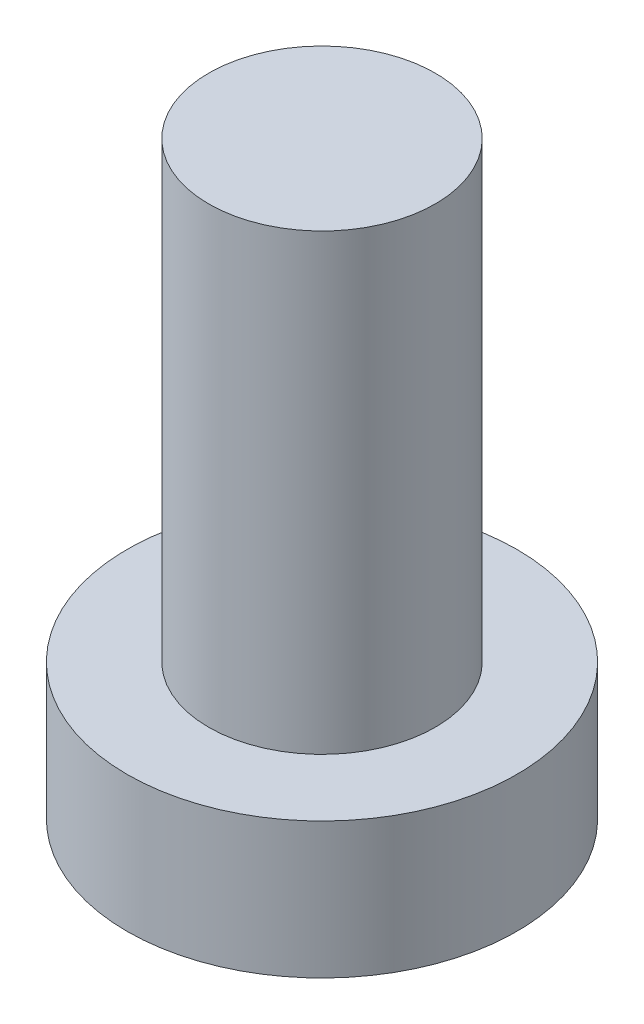
SolidWorks part; units mm, degrees
ref_plane "前视基准面" through (0, 0, 0) normal (0, 0, 1) x (1, 0, 0)
ref_plane "上视基准面" through (0, 0, 0) normal (0, 1, 0) x (1, 0, 0)
ref_plane "右视基准面" through (0, 0, 0) normal (1, 0, 0) x (0, 0, -1)
sketch "草图1" plane through (0, 0, 0) normal (0, 1, 0) x (1, 0, 0)
  circle A0 centre (0, 0) radius 4.3
extrude "凸台-拉伸1" add sketch "草图1" along normal blind 3
sketch "草图2" plane through (0, 3, 0) normal (0, 1, 0) x (1, 0, 0)
  circle A0 centre (0, 0) radius 2.5
extrude "凸台-拉伸2" add sketch "草图2" along normal blind 10
sketch "草图3" plane through (0, 0, 0) normal (0, -1, 0) x (1, 0, 0)
  line L0 (-0.6, 1.1) -> (-0.6, 2.4)
  line L1 (-2.4, -0.6) -> (-1.1, -0.6)
  line L2 (-2.4, -0.6) -> (-2.4, 0.6)
  line L3 (-2.4, 0.6) -> (-1.1, 0.6)
  line L4 (2.4, -0.6) -> (2.4, 0.6)
  line L5 (-2.4, -0.6) -> (2.4, 0.6) construction
  line L6 (-2.4, 0.6) -> (2.4, -0.6) construction
  line L7 (-0.6, -2.4) -> (0.6, -2.4)
  line L8 (-0.6, -2.4) -> (-0.6, -1.1)
  line L9 (-0.6, 2.4) -> (0.6, 2.4)
  line L10 (0.6, -2.4) -> (0.6, -1.1)
  line L11 (-0.6, -2.4) -> (0.6, 2.4) construction
  line L12 (-0.6, 2.4) -> (0.6, -2.4) construction
  line L13 (1.1, -0.6) -> (2.4, -0.6)
  line L14 (0.6, 1.1) -> (0.6, 2.4)
  line L15 (1.1, 0.6) -> (2.4, 0.6)
  arc A0 (-0.6, -1.1) -> (-1.1, -0.6) centre (-1.1, -1.1) ccw
  arc A1 (1.1, -0.6) -> (0.6, -1.1) centre (1.1, -1.1) ccw
  arc A2 (0.6, 1.1) -> (1.1, 0.6) centre (1.1, 1.1) ccw
  arc A3 (-0.6, 1.1) -> (-1.1, 0.6) centre (-1.1, 1.1) cw
  point P0 (0, 0)
  point P6 (0, 0)
  point P21 (0.6, 0.6)
  dimension "D1" = 0.5
extrude "切除-拉伸1" cut sketch "草图3" against normal blind 1.5
